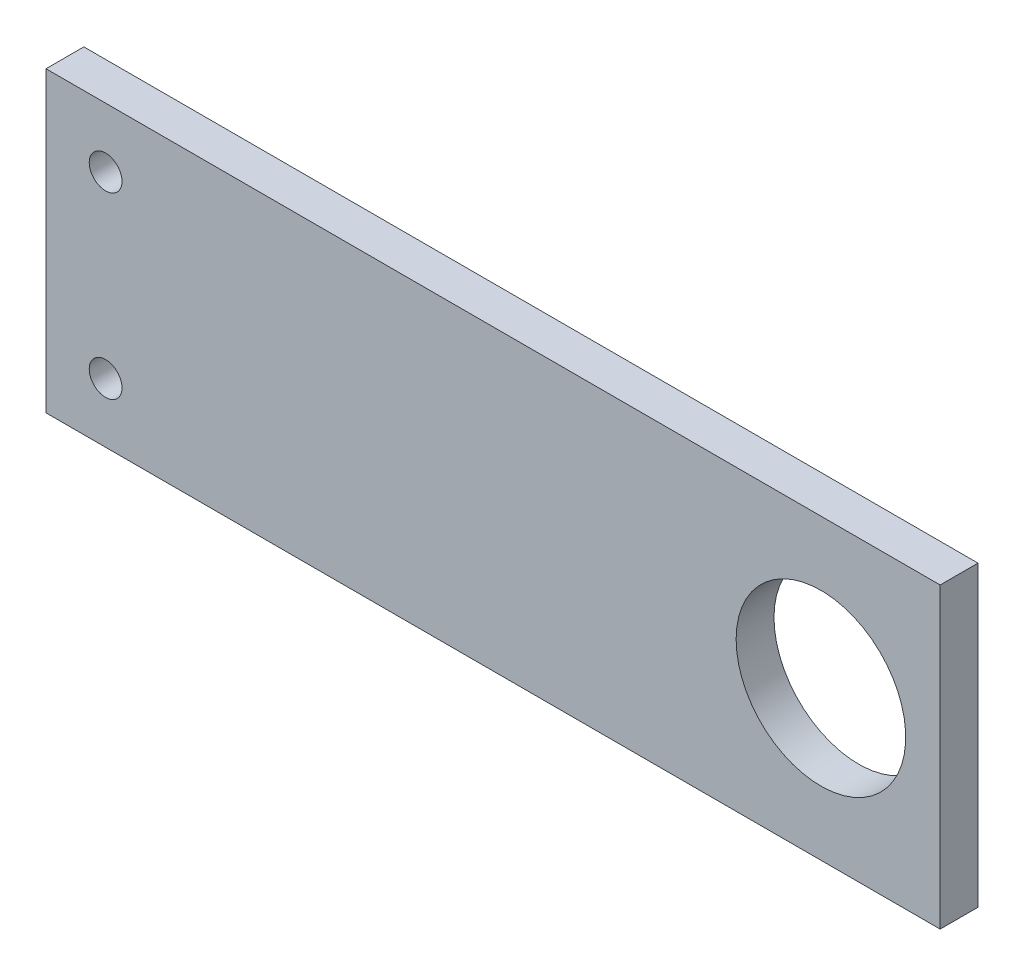
SolidWorks part; units mm, degrees
ref_plane "Front Plane" through (0, 0, 0) normal (0, 0, 1) x (1, 0, 0)
ref_plane "Top Plane" through (0, 0, 0) normal (0, 1, 0) x (1, 0, 0)
ref_plane "Right Plane" through (0, 0, 0) normal (1, 0, 0) x (0, 0, -1)
sketch "Sketch1" plane through (0, 0, 0) normal (0, 0, 1) x (1, 0, 0)
  line L1 (0, 0) -> (150, 0)
  line L2 (0, 0) -> (0, -50)
  line L3 (0, -50) -> (150, -50)
  line L4 (150, 0) -> (150, -50)
  dimension "D1" = 50
  dimension "D2" = 150
extrude "Boss-Extrude1" add sketch "Sketch1" along normal blind 6.35
sketch "Sketch2" plane through (0, 0, 0) normal (0, 0, -1) x (-1, 0, 0)
  line L0 (-150, -50) -> (-150, 0) construction
  line L1 (-150, -25) -> (-110.7339, -25) construction
  circle A0 centre (-130, -25) radius 14.225
  dimension "D1" = 28.45
  dimension "D2" = 20
extrude "Cut-Extrude1" cut sketch "Sketch2" against normal through all
sketch "Sketch3" plane through (0, 0, 0) normal (0, 0, -1) x (-1, 0, 0)
  line L0 (0, 0) -> (0, -50) construction
  line L1 (0, -50) -> (-150, -50) construction
  line L2 (-150, 0) -> (0, 0) construction
  circle A0 centre (-10, -10) radius 2.75
  circle A1 centre (-10, -40) radius 2.75
  point P6 (0, 0)
  point P11 (0, 0)
  dimension "D1" = 5.5
  dimension "D2" = 5.5
  dimension "D3" = 10
  dimension "D4" = 10
  dimension "D5" = 10
extrude "Cut-Extrude2" cut sketch "Sketch3" against normal through all
